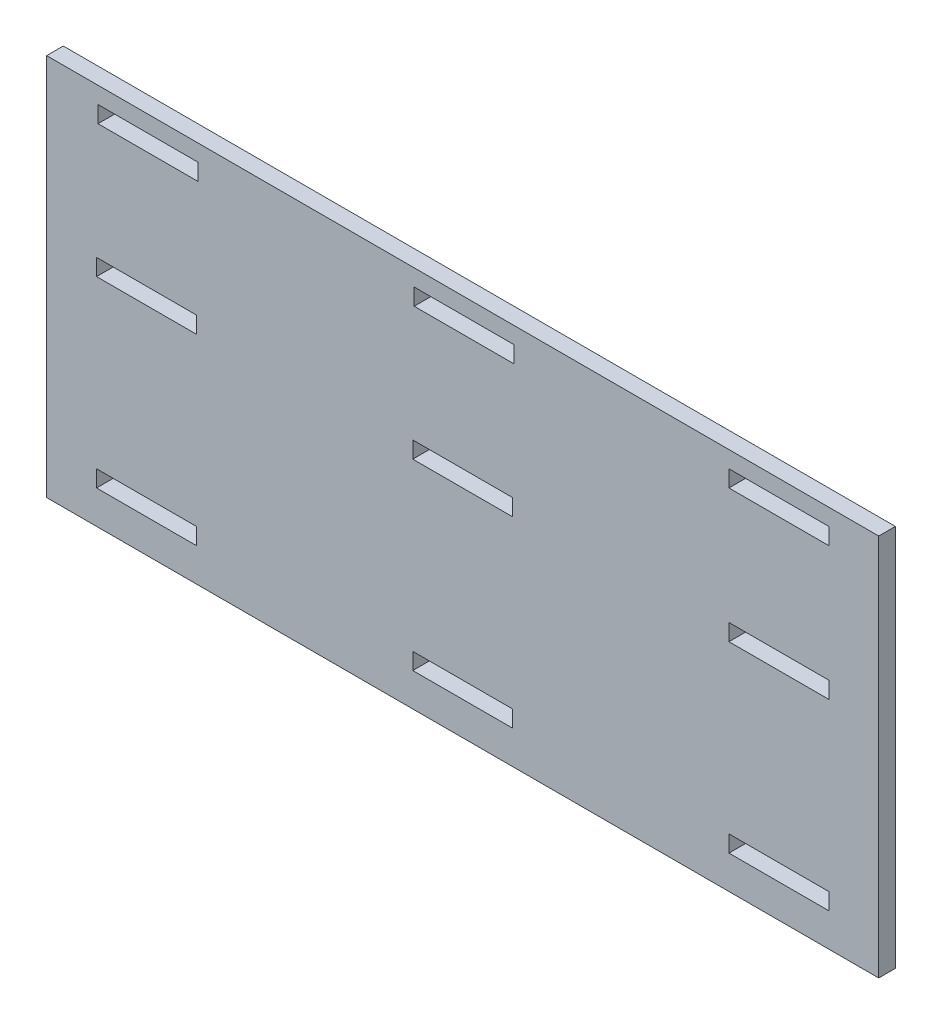
SolidWorks part; units mm, degrees
ref_plane "Front Plane" through (0, 0, 0) normal (0, 0, 1) x (1, 0, 0)
ref_plane "Top Plane" through (0, 0, 0) normal (0, 1, 0) x (1, 0, 0)
ref_plane "Right Plane" through (0, 0, 0) normal (1, 0, 0) x (0, 0, -1)
sketch "Sketch1" plane through (0, 0, 0) normal (0, 0, 1) x (1, 0, 0)
  line L0 (-120, 52.5) -> (120, 52.5) construction
  line L1 (-120, 57.5) -> (120, 57.5)
  line L2 (-120, 57.5) -> (-120, -57.5)
  line L3 (-120, -57.5) -> (120, -57.5)
  line L4 (120, 57.5) -> (120, -57.5)
  line L5 (-120, 57.5) -> (120, -57.5) construction
  line L6 (-120, -57.5) -> (120, 57.5) construction
  line L7 (-120, 12.5) -> (120, 12.5) construction
  line L8 (-120, -42.5) -> (120, -42.5) construction
  line L10 (-109.5652, 52.5) -> (-79.5652, 52.5)
  line L11 (-109.5652, 52.5) -> (-109.5652, 47.5)
  line L12 (-109.5652, 47.5) -> (-79.5652, 47.5)
  line L13 (-79.5652, 52.5) -> (-79.5652, 47.5)
  line L14 (-14.5652, 52.5) -> (15.4348, 52.5)
  line L15 (-14.5652, 52.5) -> (-14.5652, 47.5)
  line L16 (-14.5652, 47.5) -> (15.4348, 47.5)
  line L17 (15.4348, 52.5) -> (15.4348, 47.5)
  line L18 (80, 52.5) -> (110, 52.5)
  line L19 (80, 52.5) -> (80, 47.5)
  line L20 (80, 47.5) -> (110, 47.5)
  line L21 (110, 52.5) -> (110, 47.5)
  line L22 (-110, 12.5) -> (-80, 12.5)
  line L23 (-110, 12.5) -> (-110, 7.5)
  line L24 (-110, 7.5) -> (-80, 7.5)
  line L25 (-80, 12.5) -> (-80, 7.5)
  line L26 (-15, 12.5) -> (15, 12.5)
  line L27 (-15, 12.5) -> (-15, 7.5)
  line L28 (-15, 7.5) -> (15, 7.5)
  line L29 (15, 12.5) -> (15, 7.5)
  line L30 (80, 12.5) -> (110, 12.5)
  line L31 (80, 12.5) -> (80, 7.5)
  line L32 (80, 7.5) -> (110, 7.5)
  line L33 (110, 12.5) -> (110, 7.5)
  line L34 (-110, -42.5) -> (-80, -42.5)
  line L35 (-110, -42.5) -> (-110, -47.5)
  line L36 (-110, -47.5) -> (-80, -47.5)
  line L37 (-80, -42.5) -> (-80, -47.5)
  line L38 (-15, -42.5) -> (15, -42.5)
  line L39 (-15, -42.5) -> (-15, -47.5)
  line L40 (-15, -47.5) -> (15, -47.5)
  line L41 (15, -42.5) -> (15, -47.5)
  line L46 (80, -42.5) -> (110, -42.5)
  line L47 (80, -42.5) -> (80, -47.5)
  line L48 (80, -47.5) -> (110, -47.5)
  line L49 (110, -42.5) -> (110, -47.5)
  point P0 (0, 0)
  point P48 (110, 50)
  point P49 (-79.5652, 50)
  point P50 (-15, -45)
  dimension "D1" = 240
  dimension "D2" = 115
  dimension "D3" = 5
  dimension "D4" = 10
  dimension "D5" = 30
  dimension "D6" = 30
  dimension "D7" = 30
  dimension "D8" = 30
  dimension "D9" = 30
  dimension "D10" = 30
  dimension "D11" = 30
  dimension "D12" = 30
  dimension "D13" = 30
  dimension "D14" = 5
  dimension "D15" = 5
  dimension "D16" = 5
  dimension "D17" = 5
  dimension "D18" = 5
  dimension "D19" = 5
  dimension "D20" = 5
  dimension "D21" = 5
  dimension "D22" = 5
  dimension "D23" = 40
  dimension "D24" = 55
  dimension "D25" = 65
  dimension "D26" = 10.4348
  dimension "D27" = 10
  dimension "D28" = 65
  dimension "D29" = 65
  dimension "D30" = 10
  dimension "D31" = 65
  dimension "D32" = 65
sketch "Sketch2" plane through (0, 0, 0) normal (0, 0, 1) x (1, 0, 0)
  line L0 (-109.5652, 52.5) -> (-79.5652, 52.5)
  line L1 (-79.5652, 52.5) -> (-79.5652, 47.5)
  line L2 (-79.5652, 47.5) -> (-109.5652, 47.5)
  line L3 (-109.5652, 47.5) -> (-109.5652, 52.5)
  line L4 (-14.5652, 52.5) -> (15.4348, 52.5)
  line L5 (15.4348, 52.5) -> (15.4348, 47.5)
  line L6 (15.4348, 47.5) -> (-14.5652, 47.5)
  line L7 (-14.5652, 47.5) -> (-14.5652, 52.5)
  line L8 (80, 52.5) -> (110, 52.5)
  line L9 (110, 52.5) -> (110, 47.5)
  line L10 (110, 47.5) -> (80, 47.5)
  line L11 (80, 47.5) -> (80, 52.5)
  line L12 (110, 12.5) -> (110, 7.5)
  line L13 (110, 7.5) -> (80, 7.5)
  line L14 (80, 7.5) -> (80, 12.5)
  line L15 (80, 12.5) -> (110, 12.5)
  line L16 (-15, 12.5) -> (15, 12.5)
  line L17 (15, 12.5) -> (15, 7.5)
  line L18 (15, 7.5) -> (-15, 7.5)
  line L19 (-15, 7.5) -> (-15, 12.5)
  line L20 (-110, 12.5) -> (-80, 12.5)
  line L21 (-80, 12.5) -> (-80, 7.5)
  line L22 (-80, 7.5) -> (-110, 7.5)
  line L23 (-110, 7.5) -> (-110, 12.5)
  line L24 (-110, -42.5) -> (-80, -42.5)
  line L25 (-80, -42.5) -> (-80, -47.5)
  line L26 (-80, -47.5) -> (-110, -47.5)
  line L27 (-110, -47.5) -> (-110, -42.5)
  line L28 (-15, -42.5) -> (15, -42.5)
  line L29 (15, -42.5) -> (15, -47.5)
  line L30 (15, -47.5) -> (-15, -47.5)
  line L31 (-15, -47.5) -> (-15, -42.5)
  line L32 (80, -42.5) -> (110, -42.5)
  line L33 (110, -42.5) -> (110, -47.5)
  line L34 (110, -47.5) -> (80, -47.5)
  line L35 (80, -47.5) -> (80, -42.5)
  line L36 (-120, 57.5) -> (120, -57.5) construction
  line L37 (-125, 57.5) -> (125, 57.5)
  line L38 (-125, 57.5) -> (-125, -57.5)
  line L39 (-125, -57.5) -> (125, -57.5)
  line L40 (125, 57.5) -> (125, -57.5)
  line L41 (-125, 57.5) -> (125, -57.5) construction
  line L42 (-125, -57.5) -> (125, 57.5) construction
  point P70 (0, 0)
  dimension "D1" = 250
  dimension "D2" = 115
extrude "Boss-Extrude1" add sketch "Sketch2" along normal blind 5
